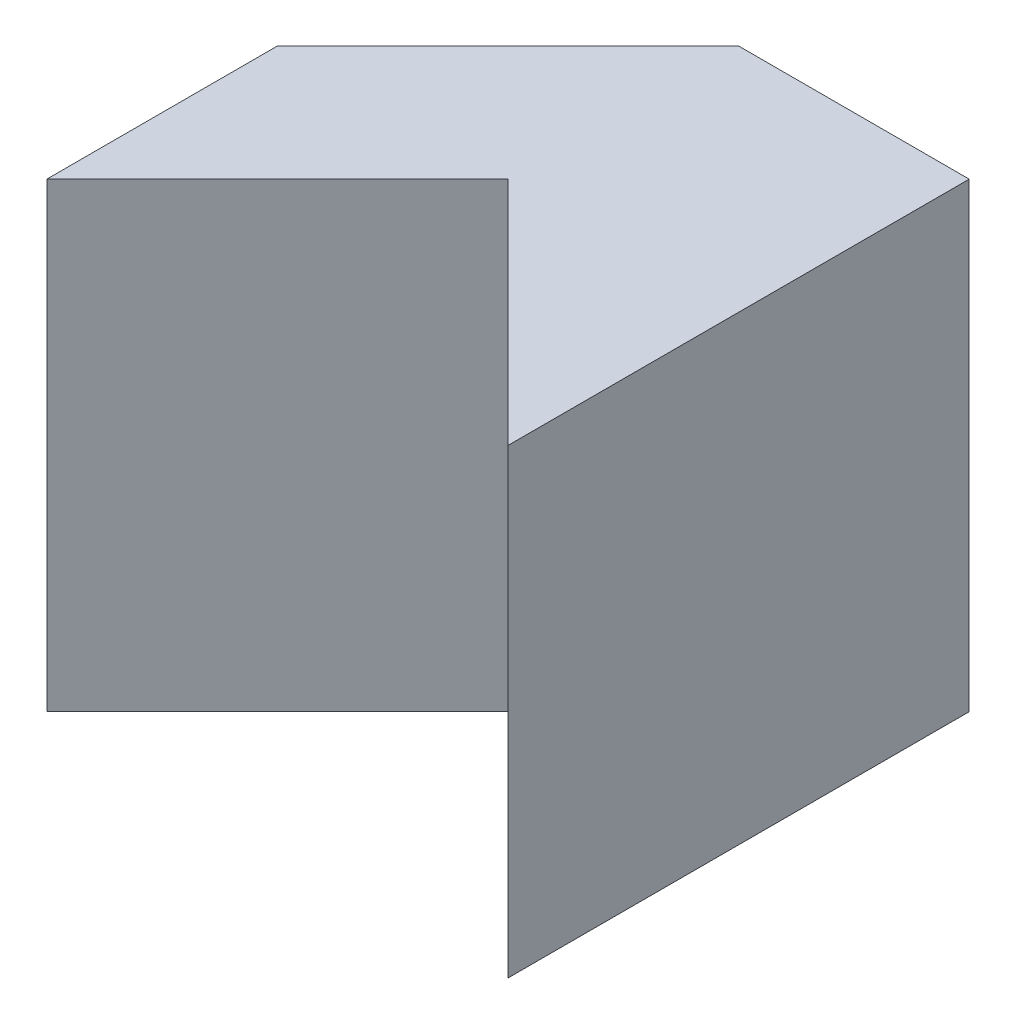
SolidWorks part; units mm, degrees
ref_plane "Front Plane" through (0, 0, 0) normal (0, 0, 1) x (1, 0, 0)
ref_plane "Top Plane" through (0, 0, 0) normal (0, 1, 0) x (1, 0, 0)
ref_plane "Right Plane" through (0, 0, 0) normal (1, 0, 0) x (0, 0, -1)
sketch "Sketch1" plane through (0, 0, 0) normal (0, 0, 1) x (1, 0, 0)
  line L1 (0, 0) -> (20, 0)
  line L2 (0, 0) -> (0, 20)
  line L3 (0, 20) -> (20, 20)
  line L4 (20, 0) -> (20, 20)
  dimension "D1" = 20
  dimension "D2" = 20
extrude "Boss-Extrude1" add sketch "Sketch1" along normal blind 20
sketch "Sketch2" plane through (0, 20, 0) normal (0, 1, 0) x (1, 0, 0)
  line L0 (0, 0) -> (10, 0)
  line L1 (20, 0) -> (0, 0) construction
  line L2 (10, 0) -> (0, -10)
  line L3 (0, -20) -> (0, 0) construction
  line L4 (0, -10) -> (0, 0)
extrude "Cut-Extrude1" cut sketch "Sketch2" against normal blind 20
sketch "Sketch3" plane through (0, 20, 0) normal (0, 1, 0) x (1, 0, 0)
  line L0 (20, -20) -> (10, -10)
  line L1 (10, -10) -> (0, -20)
  line L2 (0, -20) -> (20, -20)
  line L3 (20, -20) -> (20, 0) construction
  point P3 (20, -10)
  dimension "D1" = 10
  dimension "D2" = 10
extrude "Cut-Extrude2" cut sketch "Sketch3" against normal blind 20
